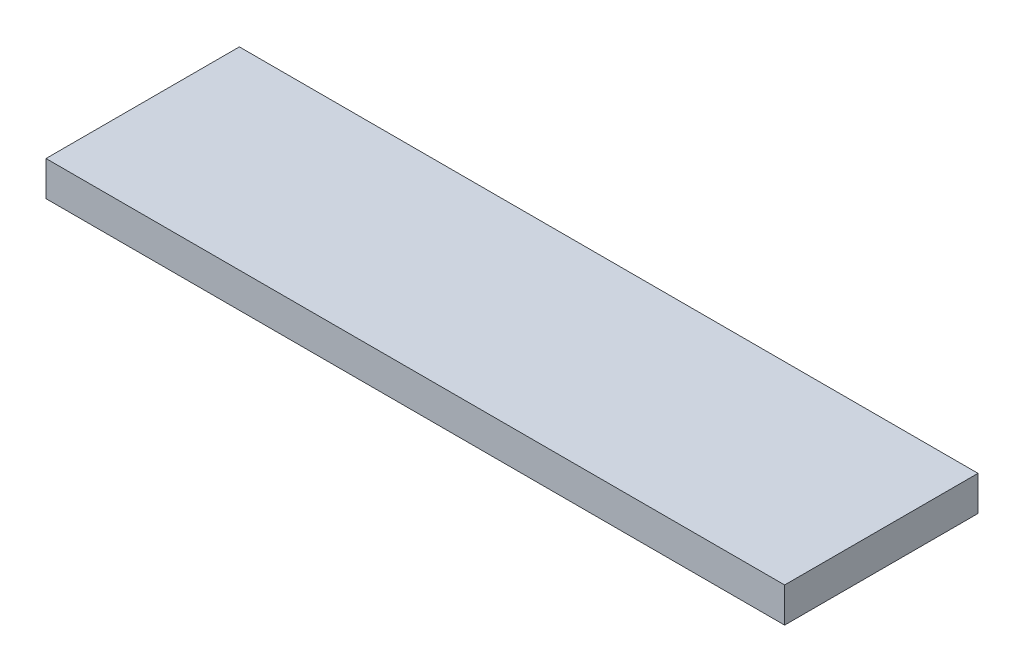
SolidWorks part; units mm, degrees
ref_plane "Front Plane" through (0, 0, 0) normal (0, 0, 1) x (1, 0, 0)
ref_plane "Top Plane" through (0, 0, 0) normal (0, 1, 0) x (1, 0, 0)
ref_plane "Right Plane" through (0, 0, 0) normal (1, 0, 0) x (0, 0, -1)
sketch "Sketch1" plane through (0, 0, 0) normal (0, 1, 0) x (1, 0, 0)
  line L1 (0, 0) -> (382, 0)
  line L2 (0, 0) -> (0, 100)
  line L3 (0, 100) -> (382, 100)
  line L4 (382, 0) -> (382, 100)
  dimension "D1" = 100
  dimension "D2" = 382
extrude "Boss-Extrude1" add sketch "Sketch1" along normal blind 18
